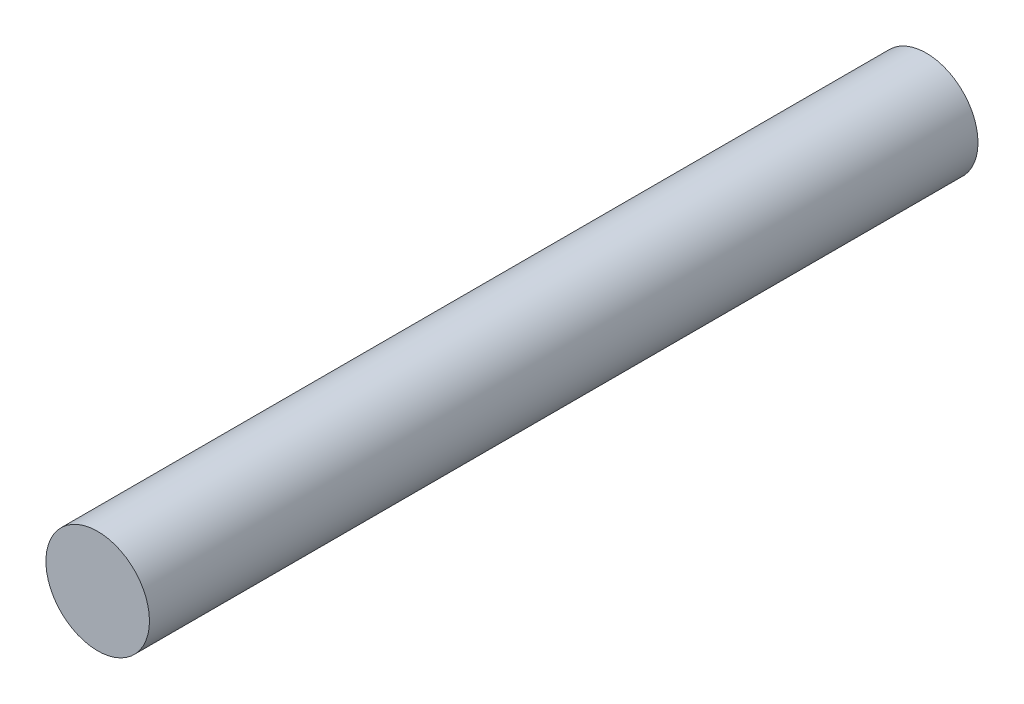
SolidWorks part; units mm, degrees
ref_plane "Front Plane" through (0, 0, 0) normal (0, 0, 1) x (1, 0, 0)
ref_plane "Top Plane" through (0, 0, 0) normal (0, 1, 0) x (1, 0, 0)
ref_plane "Right Plane" through (0, 0, 0) normal (1, 0, 0) x (0, 0, -1)
sketch "Sketch1" plane through (0, 0, 0) normal (0, 0, 1) x (1, 0, 0)
  circle A0 centre (0, 0) radius 3.175
  dimension "D1" = 6.35
extrude "Boss-Extrude1" add sketch "Sketch1" along normal blind 50.8
